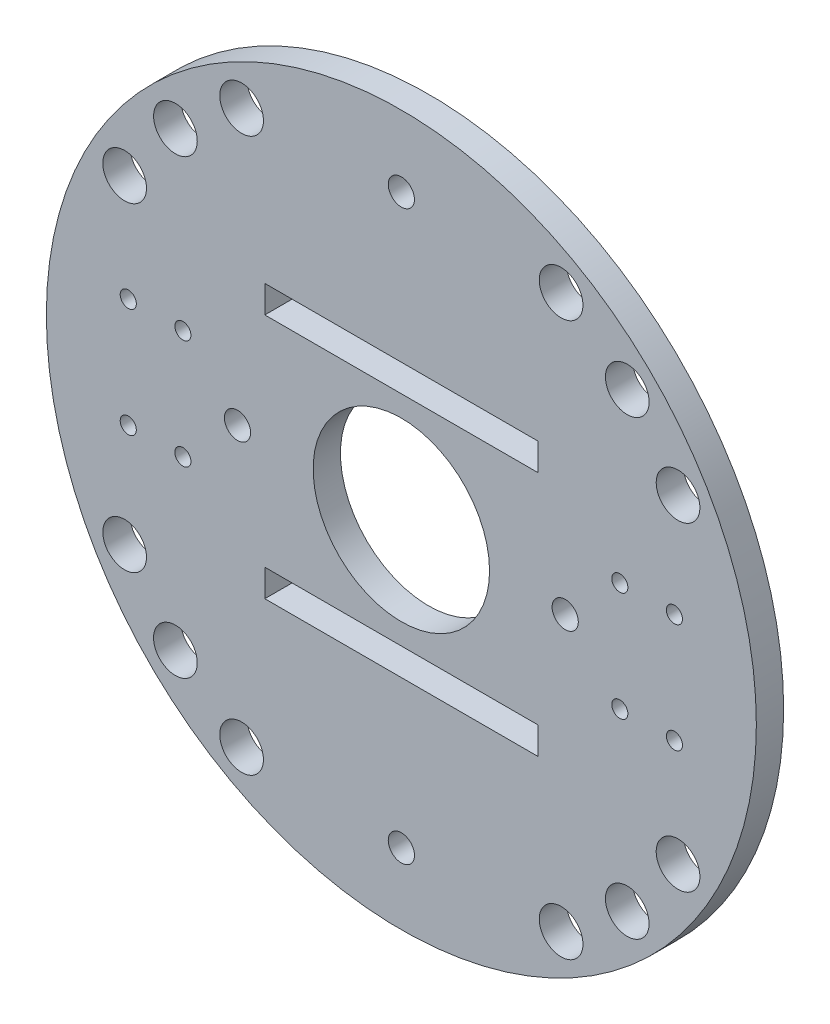
SolidWorks part; units mm, degrees
ref_plane "Front Plane" through (0, 0, 0) normal (0, 0, 1) x (1, 0, 0)
ref_plane "Top Plane" through (0, 0, 0) normal (0, 1, 0) x (1, 0, 0)
ref_plane "Right Plane" through (0, 0, 0) normal (1, 0, 0) x (0, 0, -1)
sketch "Sketch1" plane through (0, 0, 0) normal (0, 0, 1) x (1, 0, 0)
  line L0 (0, 0) -> (0, 65) construction
  line L1 (0, 0) -> (-65, 0) construction
  line L18 (0, 0) -> (-45.9619, 45.9619) construction
  line L19 (0, 0) -> (-32.5, 56.2917) construction
  line L20 (0, 0) -> (-56.2917, 32.5) construction
  line L21 (-25, -25) -> (-25, -20)
  line L22 (-25, 25) -> (25, 25)
  line L23 (-25, 25) -> (-25, 20)
  line L24 (-25, 20) -> (25, 20)
  line L25 (25, 25) -> (25, 20)
  line L26 (-25, -25) -> (25, -25)
  line L27 (25, -25) -> (25, -20)
  line L28 (-25, -20) -> (25, -20)
  circle A0 centre (0, 0) radius 65
  circle A1 centre (0, 0) radius 16.15
  circle A2 centre (0, 52) radius 2.4
  circle A3 centre (-30, 0) radius 2.4
  circle A4 centre (0, -52) radius 2.4
  circle A5 centre (30, 0) radius 2.4
  circle A6 centre (-41.3657, 41.3657) radius 4
  circle A7 centre (-29.25, 50.6625) radius 4
  circle A8 centre (-50.6625, 29.25) radius 4
  circle A9 centre (50.6625, 29.25) radius 4
  circle A10 centre (41.3657, 41.3657) radius 4
  circle A11 centre (29.25, 50.6625) radius 4
  circle A12 centre (50.6625, -29.25) radius 4
  circle A13 centre (41.3657, -41.3657) radius 4
  circle A14 centre (29.25, -50.6625) radius 4
  circle A15 centre (-29.25, -50.6625) radius 4
  circle A16 centre (-41.3657, -41.3657) radius 4
  circle A17 centre (-50.6625, -29.25) radius 4
  circle A18 centre (-40, 10) radius 1.475
  circle A19 centre (-50, 10) radius 1.475
  circle A20 centre (-40, -10) radius 1.475
  circle A21 centre (-50, -10) radius 1.475
  circle A22 centre (50, -10) radius 1.475
  circle A23 centre (40, -10) radius 1.475
  circle A24 centre (40, 10) radius 1.475
  circle A25 centre (50, 10) radius 1.475
  dimension "D1" = 130
  dimension "D2" = 32.3
  dimension "D3" = 4.8
  dimension "D5" = 4.8
  dimension "D12" = 8
  dimension "D16" = 8
  dimension "D18" = 8
  dimension "D20" = 2.95
  dimension "D23" = 2.95
  dimension "D4" = 52
  dimension "D6" = 30
  dimension "D7" = 5
  dimension "D8" = 50
  dimension "D9" = 20
  dimension "D10" = 25
  dimension "D11" = 45
  dimension "D13" = 58.5
  dimension "D14" = 15
  dimension "D15" = 15
  dimension "D17" = 58.5
  dimension "D19" = 58.5
  dimension "D21" = 40
  dimension "D22" = 10
  dimension "D24" = 10
  dimension "D25" = 10
extrude "Boss-Extrude1" add sketch "Sketch1" along normal blind 5
